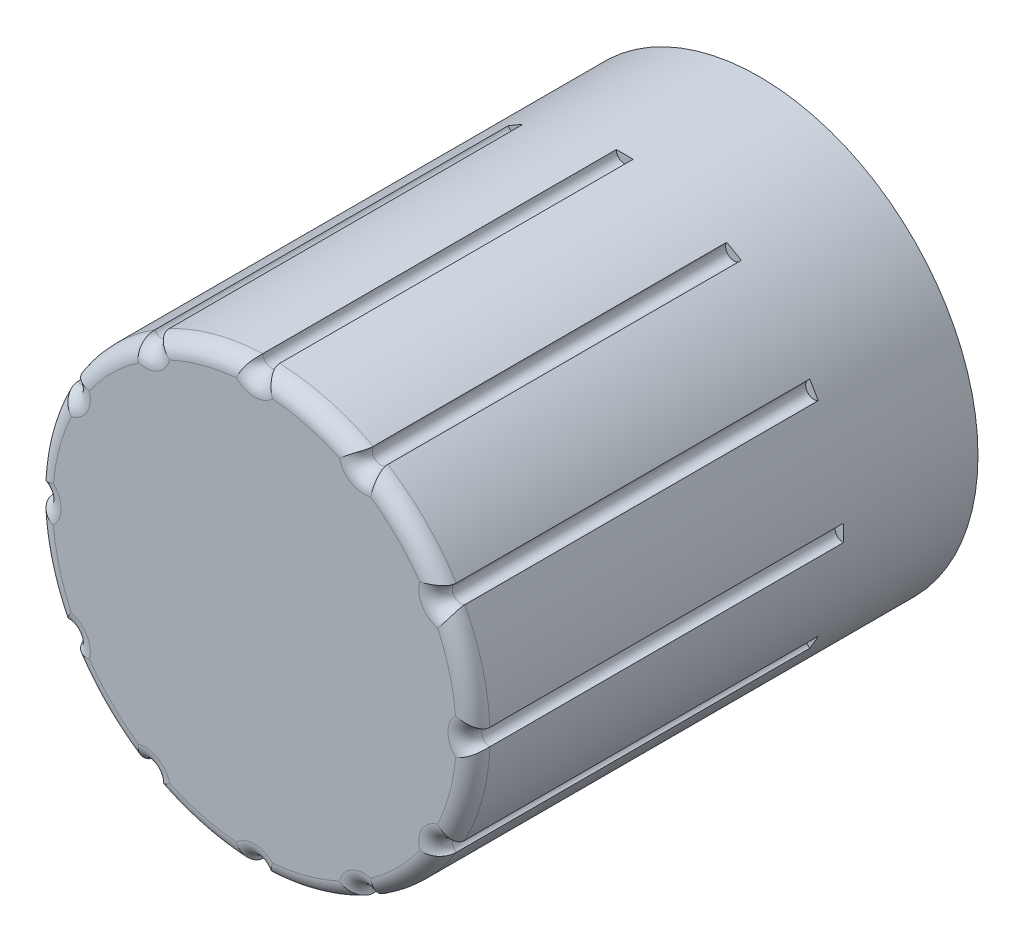
SolidWorks part; units mm, degrees
ref_plane "Ebene vorne" through (0, 0, 0) normal (0, 0, 1) x (1, 0, 0)
ref_plane "Ebene oben" through (0, 0, 0) normal (0, 1, 0) x (1, 0, 0)
ref_plane "Ebene rechts" through (0, 0, 0) normal (1, 0, 0) x (0, 0, -1)
sketch "Skizze1" plane through (0, 0, 0) normal (0, 0, 1) x (1, 0, 0)
  circle A0 centre (0, 0) radius 6.5
  point P2 (0, 0)
  dimension "D1" = 13
extrude "Aufsatz-Linear austragen1" add sketch "Skizze1" along normal blind 15
sketch "Skizze2" plane through (0, 0, 0) normal (0, 0, -1) x (-1, 0, 0)
  line L0 (-3.0594, 1.7) -> (3.0594, 1.7)
  arc A0 (-3.0594, 1.7) -> (3.0594, 1.7) centre (0, 0) ccw
  dimension "D1" = 7
  dimension "D2" = 5.2
extrude "Schnitt-Linear austragen1" cut sketch "Skizze2" against normal blind 10
sketch "Skizze3" plane through (0, 0, 15) normal (0, 0, 1) x (1, 0, 0)
  circle A0 centre (0, 6.5) radius 0.25
  circle A1 centre (0, 0) radius 6.5 construction
  circle A2 centre (3.25, 5.6292) radius 0.25
  circle A3 centre (5.6292, 3.25) radius 0.25
  circle A4 centre (6.5, 0) radius 0.25
  circle A5 centre (5.6292, -3.25) radius 0.25
  circle A6 centre (3.25, -5.6292) radius 0.25
  circle A7 centre (0, -6.5) radius 0.25
  circle A8 centre (-3.25, -5.6292) radius 0.25
  circle A9 centre (-5.6292, -3.25) radius 0.25
  circle A10 centre (-6.5, 0) radius 0.25
  circle A11 centre (-5.6292, 3.25) radius 0.25
  circle A12 centre (-3.25, 5.6292) radius 0.25
  point P28 (0, 0)
  dimension "D1" = 0.5
  dimension "D2" = 12
extrude "Schnitt-Linear austragen3" cut sketch "Skizze3" against normal blind 11
fillet "Verrundung2" radius 0.5 24 edges at (1.6823, 6.2785, 15) (3.125, 5.4127, 15) (4.5962, 4.5962, 15) (5.4127, 3.125, 15) (6.2785, 1.6823, 15) (6.25, 0, 15) (6.2785, -1.6823, 15) (5.4127, -3.125, 15) (4.5962, -4.5962, 15) (3.125, -5.4127, 15) (1.6823, -6.2785, 15) (0, -6.25, 15) (-1.6823, -6.2785, 15) (-3.125, -5.4127, 15) (-4.5962, -4.5962, 15) (-5.4127, -3.125, 15) (-6.2785, -1.6823, 15) (-6.25, 0, 15) (-6.2785, 1.6823, 15) (-5.4127, 3.125, 15) (-4.5962, 4.5962, 15) (-3.125, 5.4127, 15) (-1.6823, 6.2785, 15) (0, 6.25, 15)
